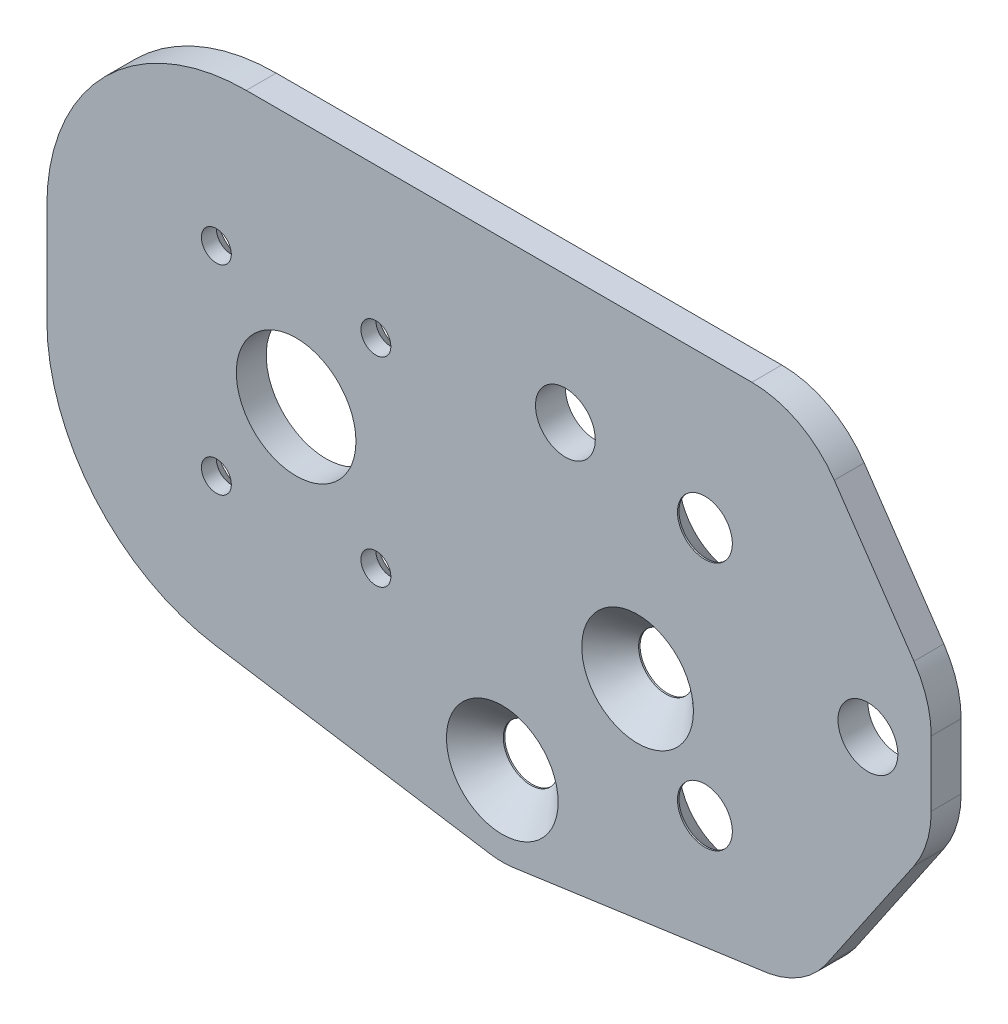
SolidWorks part; units mm, degrees
material "Gerais  - 6061-T6"
ref_plane "Plano frontal" through (0, 0, 0) normal (0, 0, 1) x (1, 0, 0)
ref_plane "Plano superior" through (0, 0, 0) normal (0, 1, 0) x (1, 0, 0)
ref_plane "Plano direito" through (0, 0, 0) normal (1, 0, 0) x (0, 0, -1)
sketch "Esboço1" plane through (0, 0, 0) normal (0, 0, 1) x (1, 0, 0)
  line L0 (56, 50) -> (56, 0) construction
  line L1 (0, 0) -> (76, 0)
  line L2 (0, 0) -> (0, 50)
  line L3 (0, 50) -> (76, 50)
  line L4 (76, 0) -> (76, 50)
  line L5 (66, 50) -> (66, 18.5) construction
  line L6 (65.25, 50) -> (65.25, 18.5) construction
  line L7 (59.25, 12.5) -> (25, 12.5) construction
  circle A0 centre (25, 25) radius 16 construction
  circle A1 centre (59.25, 18.5) radius 9.75 construction
  circle A2 centre (59.25, 18.5) radius 6 construction
  circle A3 centre (25, 25) radius 12.5 construction
  circle A4 centre (59.25, 18.5) radius 2.5
  circle A5 centre (25, 25) radius 6
  circle A6 centre (17, 38.8564) radius 1.5 construction
  circle A7 centre (33, 38.8564) radius 1.5 construction
  circle A8 centre (41, 25) radius 1.5 construction
  circle A9 centre (33, 11.1436) radius 1.5 construction
  circle A10 centre (17, 11.1436) radius 1.5 construction
  circle A11 centre (9, 25) radius 1.5 construction
  point P7 (41, 25)
  point P36 (25, 25)
  dimension "D1" = 32
  dimension "D5" = 12
  dimension "D6" = 19.5
  dimension "D9" = 25
  dimension "D10" = 5
  dimension "D13" = 12
  dimension "D14" = 3
  dimension "D2" = 25
  dimension "D3" = 35
  dimension "D4" = 20
  dimension "D7" = 0.75
  dimension "D8" = 10
  dimension "D11" = 25
  dimension "D12" = 50
  dimension "D15" = 6
extrude "Ressalto-extrusão1" add sketch "Esboço1" along normal blind 3
sketch "Esboço2" plane through (0, 0, 3) normal (0, 0, 1) x (1, 0, 0)
  line L0 (66, 50) -> (66, 0) construction
  line L1 (76, 50) -> (0, 50) construction
  line L2 (0, 0) -> (76, 0) construction
  line L3 (76, 0) -> (76, 50) construction
  circle A0 centre (66, 35) radius 2.5
  circle A1 centre (66, 10) radius 2.5
  dimension "D2" = 5
  dimension "D3" = 5
  dimension "D1" = 10
  dimension "D4" = 10
  dimension "D5" = 15
extrude "Corte-extrusão1" cut sketch "Esboço2" against normal blind 3
fillet "Filete1" radius 20 2 edges at (0, 0, 1.5) (0, 50, 1.5)
sketch "Esboço3" plane through (0, 0, 3) normal (0, 0, 1) x (1, 0, 0)
  line L1 (17, 15) -> (33, 15) construction
  line L2 (17, 15) -> (17, 35) construction
  line L3 (17, 35) -> (33, 35) construction
  line L4 (33, 15) -> (33, 35) construction
  line L5 (17, 15) -> (33, 35) construction
  line L6 (17, 35) -> (33, 15) construction
  circle A0 centre (33, 35) radius 1.5
  circle A1 centre (33, 15) radius 1.5
  circle A2 centre (17, 15) radius 1.5
  circle A3 centre (17, 35) radius 1.5
  point P0 (25, 25)
  dimension "D3" = 3
  dimension "D1" = 20
  dimension "D2" = 16
extrude "Corte-extrusão2" cut sketch "Esboço3" against normal through all
sketch "Esboço4" plane through (0, 0, 3) normal (0, 0, 1) x (1, 0, 0)
  line L0 (76, 50) -> (20, 50) construction
  line L1 (55.3323, 43.65) -> (51.6662, 50) construction
  line L2 (51.6662, 50) -> (44.3338, 50) construction
  line L3 (44.3338, 50) -> (40.6677, 43.65) construction
  line L4 (40.6677, 43.65) -> (44.3338, 37.3) construction
  line L5 (44.3338, 37.3) -> (51.6662, 37.3) construction
  line L6 (51.6662, 37.3) -> (55.3323, 43.65) construction
  line L7 (76, 0) -> (76, 50) construction
  line L8 (76, 0) -> (76, 50) construction
  line L9 (49.1263, -2.6618) -> (53.0059, 3.5567) construction
  line L10 (53.0059, 3.5567) -> (49.5604, 10.0258) construction
  line L11 (49.5604, 10.0258) -> (42.2352, 10.2764) construction
  line L12 (42.2352, 10.2764) -> (38.3556, 4.0579) construction
  line L13 (38.3556, 4.0579) -> (41.8011, -2.4112) construction
  line L14 (41.8011, -2.4112) -> (49.1263, -2.6618) construction
  line L15 (25, 12.5) -> (61.6574, 12.5) construction
  line L17 (48, 43.65) -> (45.6807, 3.8073) construction
  circle A0 centre (48, 43.65) radius 3 construction
  circle A1 centre (48, 43.65) radius 6.35 construction
  circle A2 centre (45.6807, 3.8073) radius 2.5
  circle A3 centre (45.6807, 3.8073) radius 6.35 construction
  arc A4 (17.8926, 14.7172) -> (30.3514, 13.7035) centre (25, 25) ccw construction
  arc A5 (17.8926, 14.7172) -> (30.3514, 13.7035) centre (25, 25) ccw construction
  circle A6 centre (52.0071, 37.1424) radius 3
  circle A7 centre (25, 25) radius 29.6112 construction
  circle A8 centre (59.25, 18.5) radius 2.5 construction
  circle A9 centre (59.25, 18.5) radius 2.5 construction
  dimension "D1" = 12.7
  dimension "D3" = 6
  dimension "D4" = 5
  dimension "D6" = 20
  dimension "D2" = 28
  dimension "D5" = 28
  dimension "D7" = 20
extrude "Corte-extrusão3" cut sketch "Esboço4" against normal through all
sketch "Esboço5" plane through (0, 0, 0) normal (0, 0, -1) x (-1, 0, 0)
  line L0 (-76, 0) -> (-46.7969, -4.1147)
  line L1 (-44.4359, -4.0955) -> (-16.8881, 0.2436)
  line L2 (-20, 0) -> (-76, 0) construction
  line L3 (-20, 0) -> (-76, 0) construction
  line L4 (-20, 0) -> (-76, 0)
  line L5 (-20, 0) -> (-76, 0)
  arc A1 (-46.7969, -4.1147) -> (-44.4359, -4.0955) centre (-45.6807, 3.8073) ccw
  arc A2 (-20, 0) -> (0, 20) centre (-20, 20) ccw construction
  point P1 (-45.6157, -4.1927)
  dimension "D1" = 8
extrude "Ressalto-extrusão2" add sketch "Esboço5" against normal through all
sketch "Esboço6" plane through (0, 0, 0) normal (0, 0, -1) x (-1, 0, 0)
  line L7 (-86.9656, 16.103) -> (-78.0603, 3.0256)
  line L8 (-72.4733, -0.9805) -> (-50.0089, -7.2259)
  line L9 (-46.1556, -7.2697) -> (-15.0816, 0.6142)
  line L10 (0, 20) -> (0, 30)
  line L11 (-20, 50) -> (-70.7112, 50)
  line L12 (-78.9768, 45.6286) -> (-86.9656, 33.897)
  line L13 (-88.7, 28.2685) -> (-88.7, 21.7315)
  line L14 (-86.9656, 16.103) -> (-78.0603, 3.0256)
  line L15 (-72.4733, -0.9805) -> (-50.0089, -7.2259)
  line L16 (-46.1556, -7.2697) -> (-15.0816, 0.6142)
  line L17 (0, 20) -> (0, 30)
  line L18 (-20, 50) -> (-70.7112, 50)
  line L19 (-78.9768, 45.6286) -> (-86.9656, 33.897)
  line L20 (-88.7, 28.2685) -> (-88.7, 21.7315)
  circle A0 centre (-82.35, 25) radius 3 construction
  circle A1 centre (-82.35, 25) radius 3
  arc A7 (-78.0603, 3.0256) -> (-72.4733, -0.9805) centre (-69.7947, 8.6541) ccw
  arc A8 (-50.0089, -7.2259) -> (-46.1556, -7.2697) centre (-48, 0) ccw
  arc A9 (-15.0816, 0.6142) -> (0, 20) centre (-20, 20) ccw
  arc A10 (0, 30) -> (-20, 50) centre (-20, 30) ccw
  arc A11 (-70.7112, 50) -> (-78.9768, 45.6286) centre (-70.7112, 40) ccw
  arc A12 (-86.9656, 33.897) -> (-88.7, 28.2685) centre (-78.7, 28.2685) ccw
  arc A13 (-88.7, 21.7315) -> (-86.9656, 16.103) centre (-78.7, 21.7315) ccw
  arc A15 (-50.0089, -7.2259) -> (-46.1556, -7.2697) centre (-48, 0) ccw
  arc A16 (-15.0816, 0.6142) -> (0, 20) centre (-20, 20) ccw
  arc A17 (0, 30) -> (-20, 50) centre (-20, 30) ccw
  arc A18 (-70.7112, 50) -> (-78.9768, 45.6286) centre (-70.7112, 40) ccw
  arc A19 (-86.9656, 33.897) -> (-88.7, 28.2685) centre (-78.7, 28.2685) ccw
  arc A20 (-88.7, 21.7315) -> (-86.9656, 16.103) centre (-78.7, 21.7315) ccw
  arc A54 (-78.0603, 3.0256) -> (-72.4733, -0.9805) centre (-69.7947, 8.6541) ccw
  line M16 (-76, 50) -> (-76, 0)
  dimension "D1" = 0
extrude "Ressalto-extrusão3" add sketch "Esboço6" against normal through all contours L20 A20 L14 A54 A18 L19 A19 A1 M16
sketch "Esboço7" plane through (0, 0, 0) normal (0, 0, -1) x (-1, 0, 0)
  line L0 (-76, 0) -> (-46.7969, -4.1147) construction
  line L9 (-76, 0.8122) -> (-76, 0)
  line L10 (-76, 0) -> (-46.7969, -4.1147)
  line L11 (-44.4359, -4.0955) -> (-16.8881, 0.2436)
  line L12 (0, 20) -> (0, 30)
  line L13 (-20, 50) -> (-76, 50)
  line L14 (-20, 50) -> (-76, 50)
  line L15 (-78.9768, 45.6286) -> (-86.9656, 33.897)
  line L16 (-88.7, 28.2685) -> (-88.7, 21.7315)
  line L17 (-86.9656, 16.103) -> (-78.0603, 3.0256)
  line L18 (-76, 0.8122) -> (-76, 0)
  line L19 (-76, 0) -> (-46.7969, -4.1147)
  line L20 (-44.4359, -4.0955) -> (-16.8881, 0.2436)
  line L21 (0, 20) -> (0, 30)
  line L24 (-78.9768, 45.6286) -> (-86.9656, 33.897)
  line L25 (-88.7, 28.2685) -> (-88.7, 21.7315)
  line L26 (-86.9656, 16.103) -> (-78.0603, 3.0256)
  line L28 (-76, 50) -> (-76, 48.487)
  line L29 (-76, 50) -> (-76, 48.487)
  arc A0 (-78.9768, 45.6286) -> (-70.7112, 50) centre (-70.7112, 40) cw
  arc A1 (-78.0603, 3.0256) -> (-72.4472, -0.5006) centre (-70.7403, 8.4472) ccw
  arc A7 (-46.7969, -4.1147) -> (-44.4359, -4.0955) centre (-45.6807, 3.8073) ccw
  arc A8 (-16.8881, 0.2436) -> (0, 20) centre (-20, 20) ccw
  arc A9 (0, 30) -> (-20, 50) centre (-20, 30) ccw
  arc A10 (-76, 48.487) -> (-78.9768, 45.6286) centre (-70.7112, 40) ccw
  arc A11 (-86.9656, 33.897) -> (-88.7, 28.2685) centre (-78.7, 28.2685) ccw
  arc A12 (-88.7, 21.7315) -> (-86.9656, 16.103) centre (-78.7, 21.7315) ccw
  arc A14 (-46.7969, -4.1147) -> (-44.4359, -4.0955) centre (-45.6807, 3.8073) ccw
  arc A15 (-16.8881, 0.2436) -> (0, 20) centre (-20, 20) ccw
  arc A17 (-76, 48.487) -> (-78.9768, 45.6286) centre (-70.7112, 40) ccw
  arc A18 (-86.9656, 33.897) -> (-88.7, 28.2685) centre (-78.7, 28.2685) ccw
  arc A19 (-88.7, 21.7315) -> (-86.9656, 16.103) centre (-78.7, 21.7315) ccw
  arc A22 (-78.0603, 3.0256) -> (-76, 0.8122) centre (-69.7947, 8.6541) ccw
  arc A23 (-78.0603, 3.0256) -> (-76, 0.8122) centre (-69.7947, 8.6541) ccw
  arc A24 (0, 30) -> (-20, 50) centre (-20, 30) ccw
  line M18 (-76, 0.8122) -> (-76, 0)
  line M19 (-76, 0) -> (-46.7969, -4.1147)
  line M26 (-76, 50) -> (-76, 48.487)
  dimension "D1" = 0
extrude "Corte-extrusão4" cut sketch "Esboço7" against normal through all contours A1 M18 M19 | A0 L14 M26
chamfer "Chanfro1" distance 1.5 angle 45 4 edges at (18.5, 35, 0) (18.5, 15, 0) (34.5, 15, 0) (34.5, 35, 0)
hole_wizard "Escareado para SFHCS M51" positions "Esboço16" profile "Esboço17" countersink size "M5" standard "Ansi Metric" end condition through all
sketch "Esboço16" plane through (0, 0, 3) normal (0, 0, 1) x (1, 0, 0)
  point P0 (45.6807, 3.8073)
sketch "Esboço17" plane through (45.6807, 3.8073, 3) normal (1, 0, 0) x (0, -1, 0)
  line L0 (0, 0) -> (0, 3)
  line L1 (0, 3) -> (2.75, 3)
  line L2 (2.75, 3) -> (2.75, 2.85)
  line L3 (2.75, 2.85) -> (5.6, 0)
  line L5 (5.6, 0) -> (0, 0)
  line L6 (-2.75, 2.85) -> (-5.6, 0) construction
  line L11 (0, -6.35) -> (0, 107.95) construction
  dimension "Thru Hole Dia." = 5.5
  dimension "Thru Hole Depth" = 3
  dimension "Near C'Sink Dia." = 11.2
  dimension "Near C'Sink Angle" = 90
hole_wizard "Escareado para SFHCS M52" positions "Esboço18" profile "Esboço19" countersink size "M5" standard "Ansi Metric" end condition through all
sketch "Esboço18" plane through (0, 0, 3) normal (0, 0, 1) x (1, 0, 0)
  point P0 (59.25, 18.5)
sketch "Esboço19" plane through (59.25, 18.5, 3) normal (1, 0, 0) x (0, -1, 0)
  line L0 (0, 0) -> (0, 3)
  line L1 (0, 3) -> (2.75, 3)
  line L2 (2.75, 3) -> (2.75, 2.85)
  line L3 (2.75, 2.85) -> (5.6, 0)
  line L5 (5.6, 0) -> (0, 0)
  line L6 (-2.75, 2.85) -> (-5.6, 0) construction
  line L11 (0, -6.35) -> (0, 107.95) construction
  dimension "Thru Hole Dia." = 5.5
  dimension "Thru Hole Depth" = 3
  dimension "Near C'Sink Dia." = 11.2
  dimension "Near C'Sink Angle" = 90
hole_wizard "Escareado para SFHCS M54" positions "Esboço22" profile "Esboço23" countersink size "M5" standard "Ansi Metric" end condition through all
sketch "Esboço22" plane through (0, 0, 0) normal (0, 0, -1) x (-1, 0, 0)
  point P0 (-66, 35)
  point P3 (-66, 10)
sketch "Esboço23" plane through (66, 35, 0) normal (1, 0, 0) x (0, 1, 0)
  line L0 (0, 0) -> (0, 3)
  line L1 (0, 3) -> (2.75, 3)
  line L2 (2.75, 3) -> (2.75, 2.85)
  line L3 (2.75, 2.85) -> (5.6, 0)
  line L5 (5.6, 0) -> (0, 0)
  line L6 (-2.75, 2.85) -> (-5.6, 0) construction
  line L11 (0, -6.35) -> (0, 107.95) construction
  dimension "Thru Hole Dia." = 5.5
  dimension "Thru Hole Depth" = 3
  dimension "Near C'Sink Dia." = 11.2
  dimension "Near C'Sink Angle" = 90
